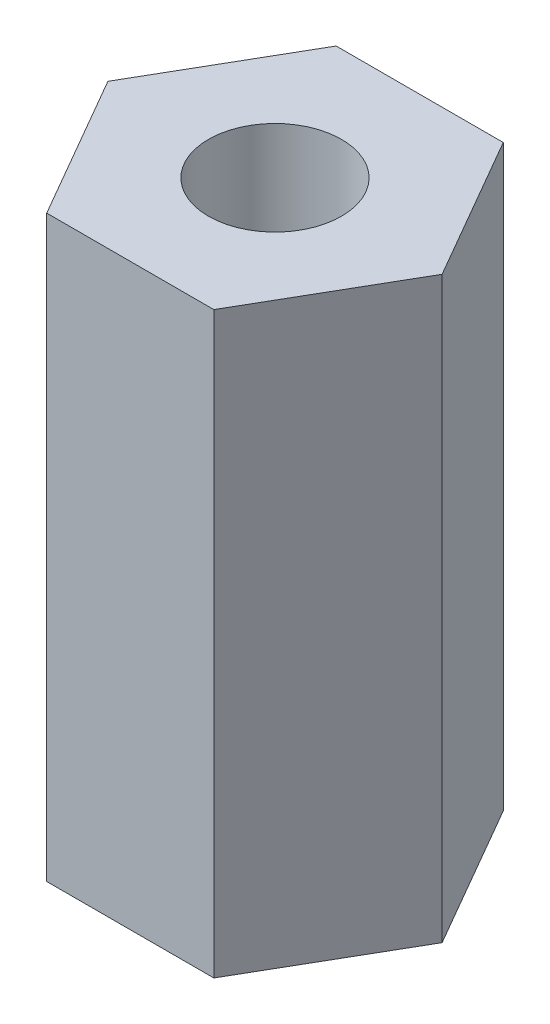
SolidWorks part; units mm, degrees
ref_plane "Front Plane" through (0, 0, 0) normal (0, 0, 1) x (1, 0, 0)
ref_plane "Top Plane" through (0, 0, 0) normal (0, 1, 0) x (1, 0, 0)
ref_plane "Right Plane" through (0, 0, 0) normal (1, 0, 0) x (0, 0, -1)
sketch "Sketch1" plane through (0, 0, 0) normal (0, 1, 0) x (1, 0, 0)
  line L1 (2.8868, 0) -> (1.4434, 2.5)
  line L2 (1.4434, 2.5) -> (-1.4434, 2.5)
  line L3 (-1.4434, 2.5) -> (-2.8868, 0)
  line L4 (-2.8868, 0) -> (-1.4434, -2.5)
  line L5 (-1.4434, -2.5) -> (1.4434, -2.5)
  line L6 (1.4434, -2.5) -> (2.8868, 0)
  circle A0 centre (0, 0) radius 2.5 construction
  circle A1 centre (0, 0) radius 1.15
  dimension "D1" = 5
  dimension "D2" = 2.3
extrude "Boss-Extrude1" add sketch "Sketch1" along normal blind 10
